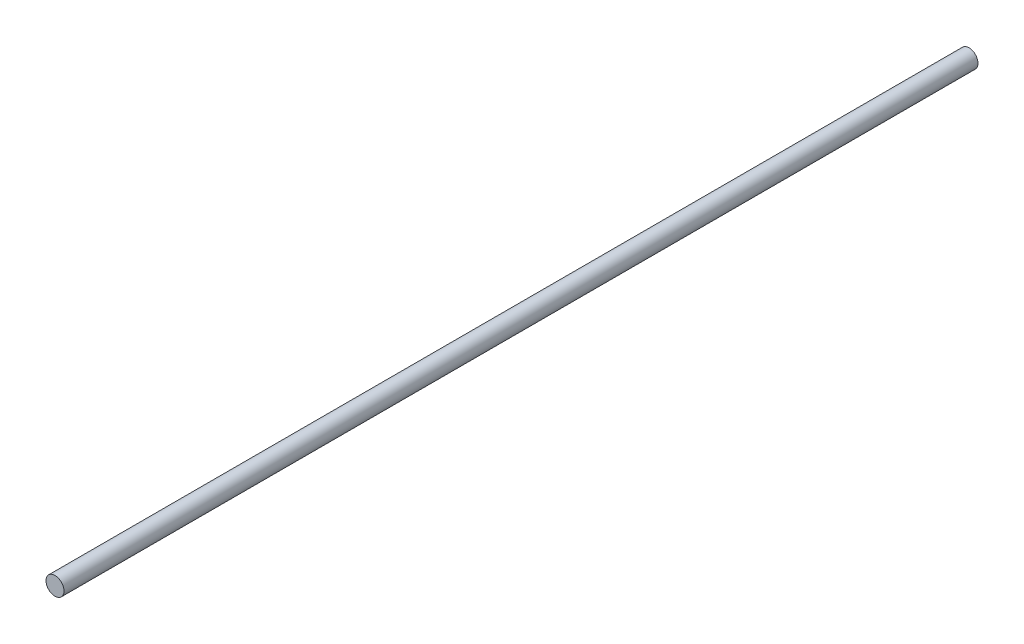
SolidWorks part; units mm, degrees
ref_plane "Front Plane" through (0, 0, 0) normal (0, 0, 1) x (1, 0, 0)
ref_plane "Top Plane" through (0, 0, 0) normal (0, 1, 0) x (1, 0, 0)
ref_plane "Right Plane" through (0, 0, 0) normal (1, 0, 0) x (0, 0, -1)
sketch "Sketch1" plane through (0, 0, 0) normal (0, 0, 1) x (1, 0, 0)
  circle A0 centre (0, 0) radius 4
extrude "Boss-Extrude1" add sketch "Sketch1" along normal blind 406
